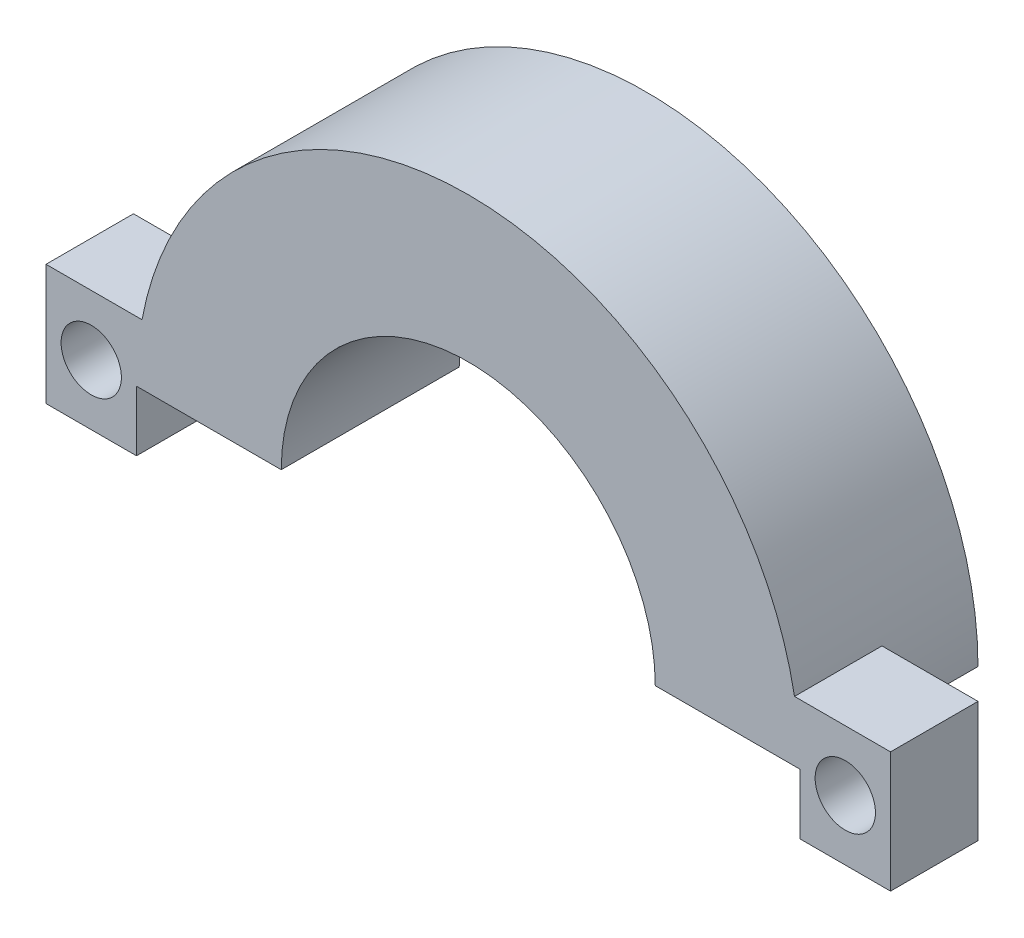
SolidWorks part; units mm, degrees
ref_plane "Plano frontal" through (0, 0, 0) normal (0, 0, 1) x (1, 0, 0)
ref_plane "Plano superior" through (0, 0, 0) normal (0, 1, 0) x (1, 0, 0)
ref_plane "Plano direito" through (0, 0, 0) normal (1, 0, 0) x (0, 0, -1)
sketch "Esboço1" plane through (0, 0, 0) normal (0, 0, 1) x (1, 0, 0)
  line L3 (-3.4368, 0) -> (18.5632, 0)
  arc A3 (-3.4368, 0) -> (18.5632, 0) centre (7.5632, 0) cw
  arc A4 (1.3632, 0) -> (13.7632, 0) centre (7.5632, 0) cw
  dimension "D2" = 6.2
  dimension "D1" = 22
extrude "Ressalto-extrusão1" add sketch "Esboço1" along normal blind 5.9 contours L3 A4 A3
sketch "Esboço2" plane through (0, 0, 5.9) normal (0, 0, 1) x (1, 0, 0)
  line L0 (18.5632, 0) -> (18.5632, -2)
  line L1 (15.5632, 2) -> (21.5632, 2)
  line L2 (15.5632, 2) -> (15.5632, -2)
  line L3 (15.5632, -2) -> (21.5632, -2)
  line L4 (21.5632, 2) -> (21.5632, -2)
  line L5 (-3.4368, 0) -> (-3.4368, -2)
  line L6 (-6.4368, 2) -> (-0.4368, 2)
  line L7 (-6.4368, 2) -> (-6.4368, -2)
  line L8 (-6.4368, -2) -> (-0.4368, -2)
  line L9 (-0.4368, 2) -> (-0.4368, -2)
  line L10 (-3.4368, 0) -> (-0.4368, 0)
  line L11 (18.5632, 0) -> (15.5632, 0)
  point P4 (21.5632, 0)
  point P12 (-6.4368, 0)
  line M5 (-3.4368, 0) -> (1.3632, 0)
  line M7 (13.7632, 0) -> (18.5632, 0)
  arc M8 (18.5632, 0) -> (-3.4368, 0) centre (7.5632, 0) ccw
  dimension "D1" = 4
  dimension "D2" = 3
  dimension "D3" = 6
  dimension "D4" = 6
  dimension "D5" = 4
  dimension "D6" = 3
extrude "Ressalto-extrusão2" add sketch "Esboço2" against normal blind 2.9 contours L7 L8 L5 L6 M8 | L9 L6 M8 M5 | L4 L1 L0 L3 M8 | L1 L2 M7 M8
sketch "Esboço3" plane through (0, 0, 5.9) normal (0, 0, 1) x (1, 0, 0)
  line L0 (21.5632, 2) -> (21.5632, -2) construction
  line L1 (-6.4368, 2) -> (-6.4368, -2) construction
  circle A0 centre (20.0632, 0) radius 1
  circle A1 centre (-4.9368, 0) radius 1
  point P8 (0, 0)
  point P9 (21.5632, 0)
  point P10 (0, 0)
  point P11 (-6.4368, 0)
  dimension "D1" = 2
  dimension "D3" = 2
  dimension "D2" = 1.5
  dimension "D4" = 1.5
  dimension "D5" = 25
extrude "Corte-extrusão1" cut sketch "Esboço3" against normal blind 6.5
